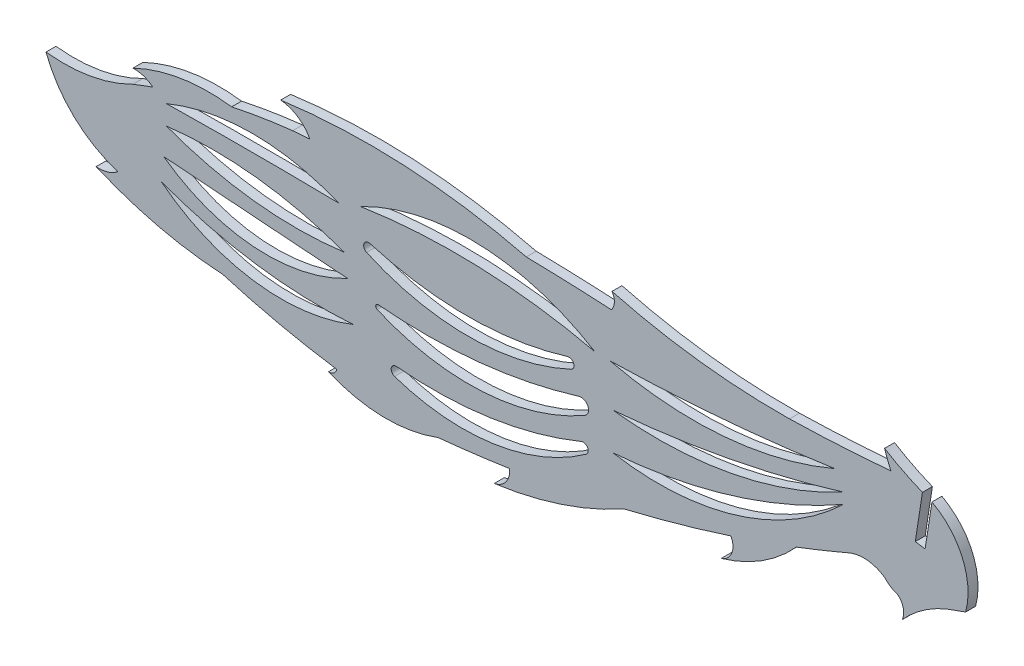
SolidWorks part; units mm, degrees
ref_plane "Front Plane" through (0, 0, 0) normal (0, 0, 1) x (1, 0, 0)
ref_plane "Top Plane" through (0, 0, 0) normal (0, 1, 0) x (1, 0, 0)
ref_plane "Right Plane" through (0, 0, 0) normal (1, 0, 0) x (0, 0, -1)
sketch "Model" plane through (0, 0, 0) normal (0, 0, 1) x (1, 0, 0)
  line L0 (126.365, 30.737) -> (125.1142, 22.6516) construction
  line L1 (125.4574, 29.8547) -> (124.3612, 22.7681)
  line L2 (126.9145, 29.3047) -> (125.8673, 22.5351)
  line L4 (124.3612, 22.7681) -> (125.8673, 22.5351)
  line L5 (125.6119, 30.8535) -> (124.3612, 22.7681) construction
  line L6 (127.118, 30.6205) -> (125.8673, 22.5351) construction
  line L123 (132.0808, 17.2754) -> (129.2015, 16.2312)
  arc A1 (119.655, 32.7944) -> (120.6241, 30.2797) centre (140.8446, 39.5163) ccw
  arc A2 (105.0839, 29.4139) -> (77.8778, 32.7353) centre (103.7063, 131.2147) cw
  arc A3 (77.8778, 32.7353) -> (77.7776, 30.2466) centre (76.1605, 31.5581) cw
  arc A4 (64.7497, 30.737) -> (27.0955, 32.7353) centre (40.7026, -66.6251) ccw
  arc A5 (27.0955, 32.7353) -> (31.5734, 29.7989) centre (26.6528, 27.1776) cw
  arc A6 (31.5734, 29.7989) -> (28.9288, 29.5886) centre (58.0674, -320.0647) ccw
  arc A7 (19.5882, 28.0822) -> (4.4589, 25.6613) centre (16.0799, 1.5221) ccw
  arc A8 (4.4589, 25.6613) -> (7.5081, 24.6603) centre (4.6423, 21.0751) cw
  arc A9 (7.5081, 24.6603) -> (4.4589, 23.5146) centre (39.3416, -64.6877) ccw
  arc A10 (113.3444, 22.1962) -> (77.9904, 11.3865) centre (85.0429, 51.5398) cw
  arc A11 (77.9904, 11.3865) -> (113.3444, 22.1962) centre (71.7807, 94.9153) ccw
  arc A12 (2.1294, 10.7511) -> (-8.8663, 21.1325) centre (7.298, 27.2394) cw
  arc A13 (-8.8663, 21.1325) -> (4.4589, 23.5146) centre (-6.1591, 44.4505) ccw
  arc A14 (113.3444, 23.8208) -> (77.9904, 17.0437) centre (84.8883, 76.6639) cw
  arc A15 (77.9904, 17.0437) -> (113.3444, 23.8208) centre (63.9998, 185.6329) ccw
  arc A16 (112.01, 26.2737) -> (77.6132, 23.3639) centre (90.401, 76.9568) cw
  arc A17 (112.01, 26.2737) -> (77.6132, 23.3639) centre (71.1125, 304.9632) cw
  arc A18 (73.9204, 9.1442) -> (44.5527, 4.7814) centre (54.9716, 35.6719) cw
  arc A19 (44.8676, 6.258) -> (44.5527, 4.7814) centre (44.7956, 5.5015) ccw
  arc A20 (73.9204, 9.1442) -> (73.1899, 10.4655) centre (73.4787, 9.7626) ccw
  arc A21 (73.7172, 14.1909) -> (72.8099, 16.2737) centre (73.1472, 15.1816) ccw
  arc A22 (42.0825, 13.0585) -> (41.8977, 12.3289) centre (42.0479, 12.6791) ccw
  arc A23 (71.616, 19.2633) -> (71.0698, 20.6822) centre (71.2941, 19.9539) ccw
  arc A24 (71.616, 19.2633) -> (40.2609, 19.1088) centre (55.7706, 53.2676) cw
  arc A25 (40.7931, 20.5331) -> (40.2609, 19.1088) centre (40.576, 19.8027) ccw
  arc A26 (75.2499, 23.4198) -> (39.3416, 24.7371) centre (53.8476, -69.9164) ccw
  arc A27 (38.2181, 8.5094) -> (8.7994, 12.7634) centre (33.38, 78.9001) cw
  arc A28 (38.2181, 8.5094) -> (8.7994, 12.7634) centre (27.1804, 36.0274) cw
  arc A29 (37.3663, 14.1909) -> (9.1844, 16.2737) centre (578.4232, 7526.735) cw
  arc A30 (75.2499, 23.4198) -> (39.3416, 24.7371) centre (56.1249, -7.8384) ccw
  arc A31 (37.3663, 14.1909) -> (9.1844, 16.2737) centre (24.9433, 37.8005) cw
  arc A32 (36.8481, 17.4136) -> (9.5963, 20.5331) centre (29.4735, 73.5855) cw
  arc A33 (36.8481, 17.4136) -> (9.5963, 20.5331) centre (16.7849, -37.2641) ccw
  arc A34 (35.9416, 23.5146) -> (9.5963, 23.5146) centre (22.7689, -737.9097) ccw
  arc A35 (9.5963, 23.5146) -> (35.9416, 23.5146) centre (22.7689, -8.1397) cw
  arc A36 (129.2015, 16.2312) -> (122.3426, 11.3865) centre (136.1962, -0.9492) ccw
  arc A37 (122.3426, 11.3865) -> (121.6378, 14.3951) centre (120.1266, 12.4542) ccw
  arc A38 (106.1164, 12.9157) -> (94.6123, 5.6577) centre (87.6223, 29.4831) cw
  arc A39 (94.6123, 5.6577) -> (96.0883, 9.3784) centre (93.8351, 8.1191) ccw
  arc A40 (79.7389, 4.7814) -> (59.8253, -1.7849) centre (52.2575, 54.6457) cw
  arc A41 (59.8253, -1.7849) -> (62.1772, 1.3676) centre (59.3236, 1.043) ccw
  arc A42 (51.2039, 0.0016) -> (34.4303, 0.3491) centre (43.2461, 20.8844) cw
  arc A43 (34.4303, 0.3491) -> (35.6963, 1.2959) centre (34.5272, 1.5393) ccw
  arc A44 (18.2423, 5.157) -> (-1.1865, 9.7626) centre (21.6438, 62.7892) cw
  arc A45 (-1.1865, 9.7626) -> (2.1294, 10.7511) centre (-0.749, 14.351) ccw
  arc A46 (79.7389, 4.7814) -> (96.0883, 9.3784) centre (30.4578, 211.4217) ccw
  arc A47 (106.1164, 12.9157) -> (114.1114, 16.1503) centre (30.4578, 211.4217) ccw
  arc A50 (125.4574, 29.8547) -> (119.655, 32.7944) centre (139.3783, 64.5287) cw
  arc A51 (126.9145, 29.3047) -> (132.0808, 17.2754) centre (121.9268, 20.0385) cw
  arc A436 (77.7776, 30.2466) -> (64.7497, 30.737) centre (58.0674, -320.0647) ccw
  arc A437 (105.0839, 29.4139) -> (120.6241, 30.2797) centre (99.3935, 271.4491) ccw
  arc A442 (18.2423, 5.157) -> (35.6963, 1.2959) centre (53.7816, 124.4326) ccw
  arc A452 (28.9288, 29.5886) -> (19.5882, 28.0822) centre (39.3416, -64.6877) ccw
  arc A459 (51.2039, 0.0016) -> (62.1772, 1.3676) centre (30.4578, 211.4217) ccw
  arc A474 (44.8676, 6.258) -> (73.1899, 10.4655) centre (50.5196, 65.6398) ccw
  arc A475 (41.8977, 12.3289) -> (73.7172, 14.1909) centre (55.9455, 45.0791) ccw
  arc A476 (42.0825, 13.0585) -> (72.8099, 16.2737) centre (49.3189, 92.3376) ccw
  arc A477 (40.7931, 20.5331) -> (71.0698, 20.6822) centre (55.685, 70.6374) ccw
  arc A512 (119.655, 15.6682) -> (121.6378, 14.3951) centre (122.9089, 18.5551) ccw
  arc A515 (119.655, 15.6682) -> (114.1114, 16.1503) centre (116.4492, 10.9179) ccw
  dimension "D1" = 1.143
  dimension "D2" = 0.381
  dimension "D3" = 0.762
  dimension "D4" = 0.762
  dimension "D5" = 0.762
  dimension "D6" = 0.762
extrude "Boss-Extrude1" add sketch "Model" along normal blind 1.524
